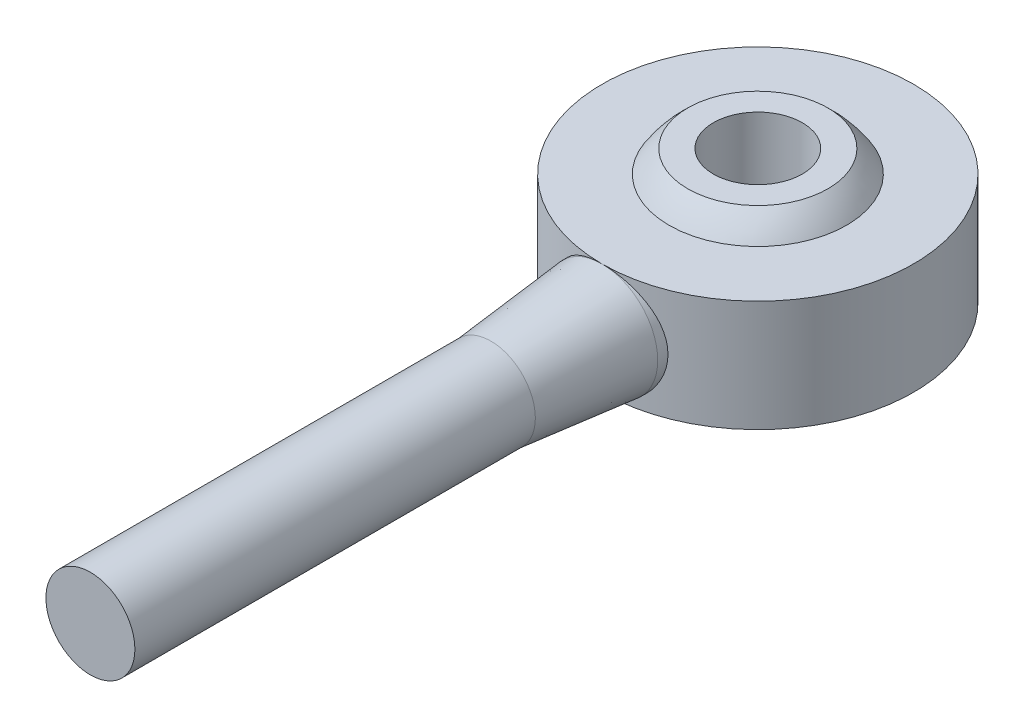
SolidWorks part; units mm, degrees
ref_plane "Front Plane" through (0, 0, 0) normal (0, 0, 1) x (1, 0, 0)
ref_plane "Top Plane" through (0, 0, 0) normal (0, 1, 0) x (1, 0, 0)
ref_plane "Right Plane" through (0, 0, 0) normal (1, 0, 0) x (0, 0, -1)
sketch "Sketch1" plane through (0, 0, 0) normal (0, 1, 0) x (1, 0, 0)
  circle A0 centre (0, 0) radius 7
  circle A1 centre (0, 0) radius 3.25
  dimension "D1" = 14
  dimension "D2" = 6.5
extrude "Boss-Extrude1" add sketch "Sketch1" along normal mid plane 5
sketch "Sketch2" plane through (0, 0, 0) normal (1, 0, 0) x (0, 0, -1)
  line L0 (0, 6) -> (0, -6) construction
  line L1 (-3.15, 3.5) -> (-2, 3.5)
  line L2 (-2, 3.5) -> (-2, -3.5)
  line L3 (-2, -3.5) -> (-3.15, -3.5)
  line L4 (-2, 0) -> (0, 0) construction
  arc A0 (-3.15, 3.5) -> (-3.15, -3.5) centre (0, 0) ccw
  dimension "D1" = 7
  dimension "D2" = 4
  dimension "D3" = 6.3
revolve "Revolve1" add sketch "Sketch2" angle 360 about L0
sketch "Sketch3" plane through (0, 0, 0) normal (1, 0, 0) x (0, 0, -1)
  line L0 (-12, 2) -> (-7, 2.5)
  line L1 (-30, 0) -> (-5, 0)
  line L2 (-30, 0) -> (-30, 2)
  line L3 (-30, 2) -> (-12, 2)
  line L4 (-5, 0) -> (-5, 2.5)
  line L5 (-7, 2.5) -> (-5, 2.5)
  dimension "D1" = 5
  dimension "D2" = 2
  dimension "D3" = 30
  dimension "D4" = 18
revolve "Revolve2" add sketch "Sketch3" angle 360 about L1
